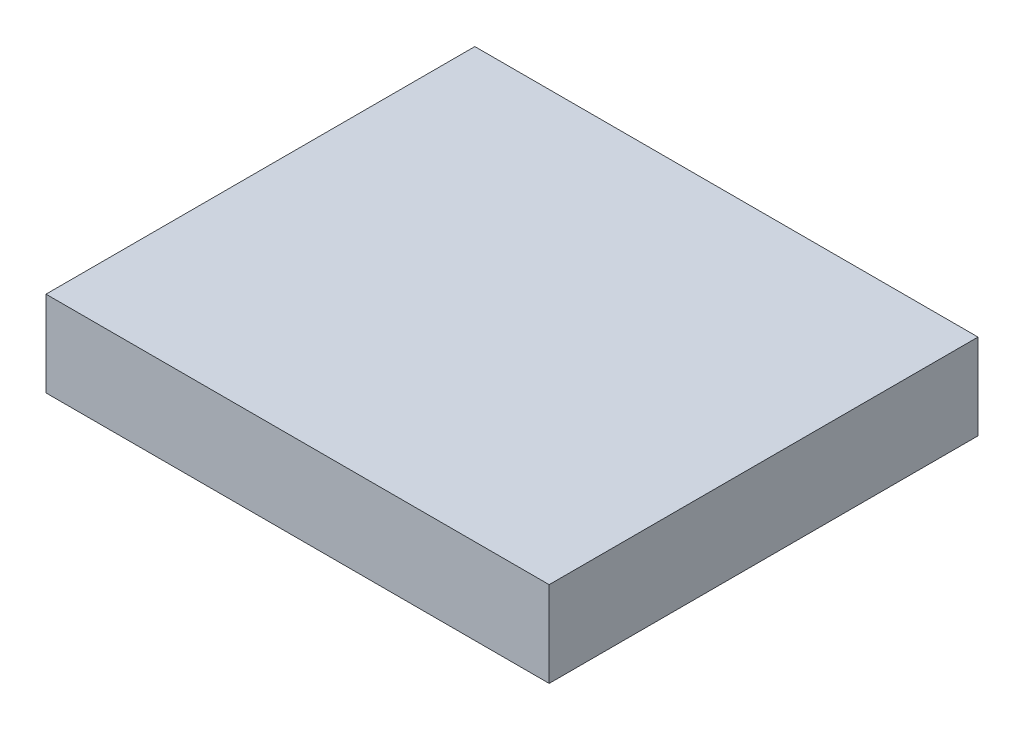
SolidWorks part; units mm, degrees
ref_plane "Alzado" through (0, 0, 0) normal (0, 0, 1) x (1, 0, 0)
ref_plane "Planta" through (0, 0, 0) normal (0, 1, 0) x (1, 0, 0)
ref_plane "Vista lateral" through (0, 0, 0) normal (1, 0, 0) x (0, 0, -1)
sketch "Croquis1" plane through (0, 0, 0) normal (0, 1, 0) x (1, 0, 0)
  line L1 (0, 0) -> (58.8037, 0)
  line L2 (0, 0) -> (0, 50.1175)
  line L3 (0, 50.1175) -> (58.8037, 50.1175)
  line L4 (58.8037, 0) -> (58.8037, 50.1175)
extrude "Saliente-Extruir1" add sketch "Croquis1" along normal blind 10
